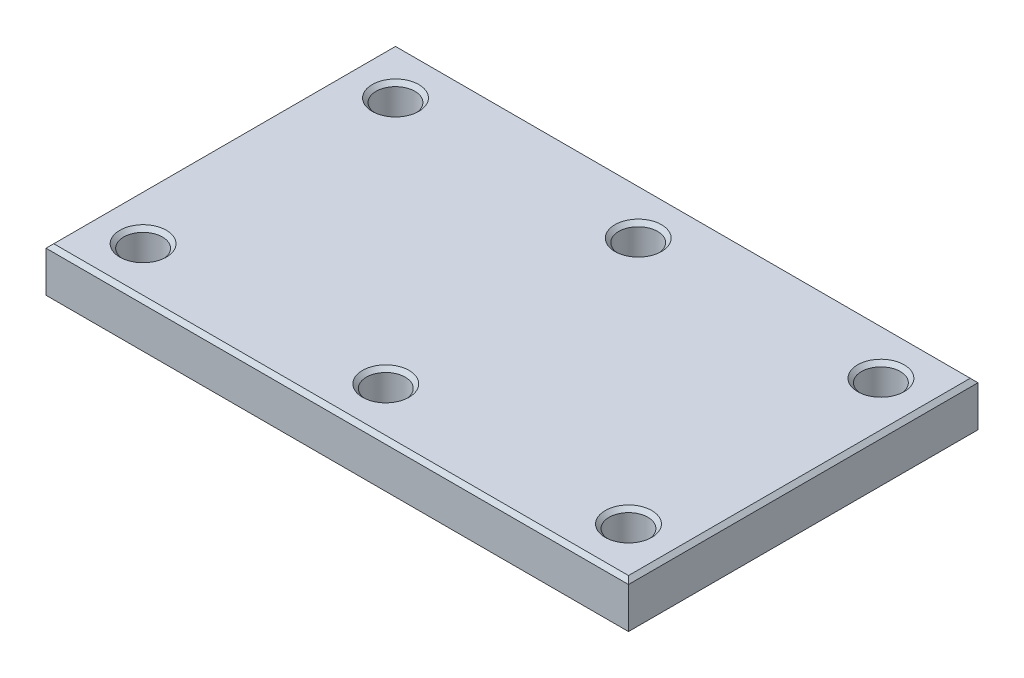
SolidWorks part; units mm, degrees
ref_plane "Front Plane" through (0, 0, 0) normal (0, 0, 1) x (1, 0, 0)
ref_plane "Top Plane" through (0, 0, 0) normal (0, 1, 0) x (1, 0, 0)
ref_plane "Right Plane" through (0, 0, 0) normal (1, 0, 0) x (0, 0, -1)
sketch "Sketch1" plane through (0, 0, 0) normal (0, 1, 0) x (1, 0, 0)
  line L1 (-150, -90) -> (150, -90)
  line L2 (-150, -90) -> (-150, 90)
  line L3 (-150, 90) -> (150, 90)
  line L4 (150, -90) -> (150, 90)
  point P0 (0, 0)
  dimension "D1" = 300
  dimension "D2" = 180
extrude "Boss-Extrude1" add sketch "Sketch1" along normal mid plane 25
sketch "Sketch2" plane through (0, 12.5, 0) normal (0, 1, 0) x (1, 0, 0)
  circle A2 centre (-125, 65) radius 10
  circle A3 centre (0, 65) radius 10
  circle A4 centre (125, 65) radius 10
  circle A5 centre (0, -65) radius 10
  circle A6 centre (125, -65) radius 10
  circle A7 centre (-125, -65) radius 10
  point P4 (0, 0)
  dimension "D2" = 3
  dimension "D3" = 2
extrude "Cut-Extrude1" cut sketch "Sketch2" against normal blind 25
chamfer "Chamfer1" distance 2 angle 45 10 edges at (0, 12.5, 90) (-150, 12.5, 0) (0, 12.5, -90) (150, 12.5, 0) (-125, 12.5, -55) (0, 12.5, -55) (125, 12.5, -55) (0, 12.5, 75) (125, 12.5, 75) (-125, 12.5, 75)
chamfer "Chamfer2" distance 2 angle 45 10 edges at (0, -12.5, -90) (-150, -12.5, 0) (0, -12.5, 90) (150, -12.5, 0) (-125, -12.5, -55) (0, -12.5, -55) (125, -12.5, -55) (0, -12.5, 75) (125, -12.5, 75) (-125, -12.5, 75)
